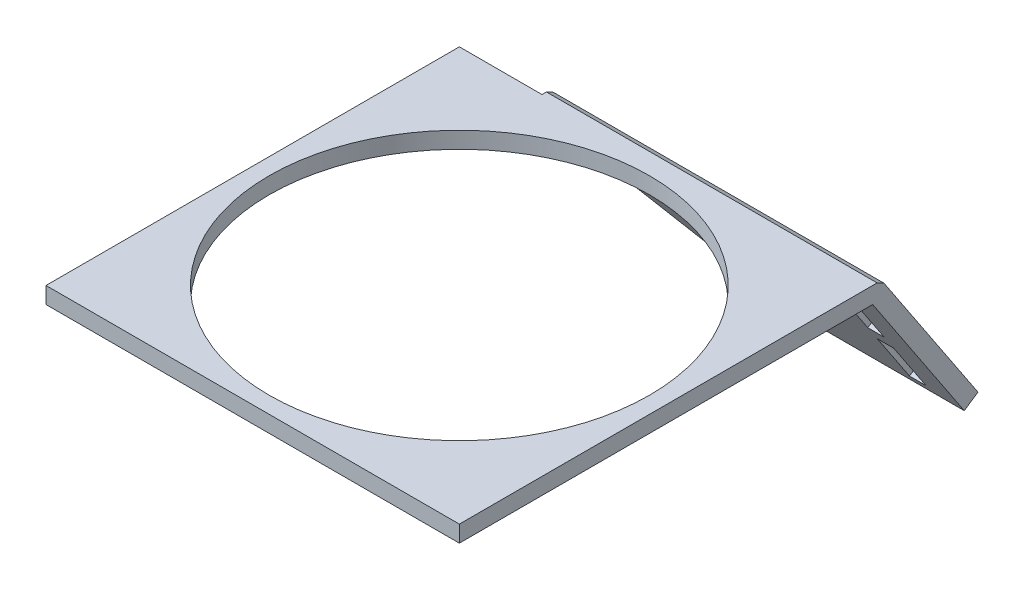
SolidWorks part; units mm, degrees
ref_plane "Front Plane" through (0, 0, 0) normal (0, 0, 1) x (1, 0, 0)
ref_plane "Top Plane" through (0, 0, 0) normal (0, 1, 0) x (1, 0, 0)
ref_plane "Right Plane" through (0, 0, 0) normal (1, 0, 0) x (0, 0, -1)
sketch "Sketch1" plane through (0, 0, 0) normal (0, 1, 0) x (1, 0, 0)
  line L0 (-40, 15.1776) -> (0, -24.8224) construction
  line L1 (-40, 15.1776) -> (0, 15.1776)
  line L2 (-40, 15.1776) -> (-40, -24.8224)
  line L3 (-40, -24.8224) -> (0, -24.8224)
  line L4 (0, 15.1776) -> (0, -24.8224)
  line L5 (0, -24.8224) -> (-0.0735, -24.5293) construction
  circle A0 centre (-20, -4.8224) radius 19
  dimension "D3" = 38
  dimension "D1" = 40
  dimension "D2" = 40
extrude "Boss-Extrude1" add sketch "Sketch1" along normal blind 1
sketch "Sketch2" plane through (0, 0, 0) normal (1, 0, 0) x (0, 0, -1)
  line L0 (15.1776, 0) -> (26.2516, -16.6543)
  line L1 (26.2516, -16.6543) -> (27.0843, -16.1006)
  line L2 (27.0843, -16.1006) -> (15.7136, 1)
  line L3 (15.7136, 1) -> (15.1776, 1)
  line L4 (15.1776, 1) -> (15.1776, 0)
  dimension "D1" = 1
  dimension "D2" = 1
  dimension "D3" = 20
extrude "Boss-Extrude3" add sketch "Sketch2" against normal blind 40
sketch "Sketch3" plane through (0, 6.998, -10.5244) normal (0, -0.5537, 0.8327) x (1, 0, 0)
  line L0 (-20, -28.4038) -> (-40, -8.4038)
  line L1 (-40, -28.4038) -> (0, -28.4038) construction
  line L2 (-40, -8.4038) -> (-40, -28.4038)
  line L3 (-40, -28.4038) -> (-20, -28.4038)
extrude "Cut-Extrude1" cut sketch "Sketch3" against normal blind 40
sketch "Sketch4" plane through (0, 6.998, -10.5244) normal (0, -0.5537, 0.8327) x (1, 0, 0)
  line L0 (-5, -8.4038) -> (-5, -28.4038) construction
  line L1 (0, -8.4038) -> (-40, -8.4038) construction
  line L2 (-20, -28.4038) -> (0, -28.4038) construction
  line L3 (0, -8.4038) -> (0, -28.4038) construction
  line L5 (-4, -27.2711) -> (-6, -27.2711)
  line L6 (-4, -27.2711) -> (-4, -9.3119)
  line L7 (-4, -9.3119) -> (-6, -9.3119)
  line L8 (-6, -27.2711) -> (-6, -9.3119)
  dimension "D1" = 5
  dimension "D2" = 1
  dimension "D3" = 1
extrude "Cut-Extrude2" cut sketch "Sketch4" against normal blind 40
sketch "Sketch5" plane through (0, 6.998, -10.5244) normal (0, -0.5537, 0.8327) x (1, 0, 0)
  line L1 (-3.0456, -20.2228) -> (-7.3369, -20.2228)
  line L2 (-3.0456, -20.2228) -> (-3.0456, -18.1628)
  line L3 (-3.0456, -18.1628) -> (-7.3369, -18.1628)
  line L4 (-7.3369, -20.2228) -> (-7.3369, -18.1628)
extrude "Boss-Extrude4" add sketch "Sketch5" against normal blind 1
sketch "Sketch6" plane through (0, 1, 0) normal (0, 1, 0) x (1, 0, 0)
  line L1 (-40, -24.8224) -> (0, -24.8224)
  line L2 (-40, -24.8224) -> (-40, 15.7136)
  line L3 (-40, 15.7136) -> (0, 15.7136)
  line L4 (0, -24.8224) -> (0, 15.7136)
  circle A0 centre (-20, -4.8224) radius 19
extrude "Boss-Extrude5" add sketch "Sketch6" along normal blind 1
sketch "Sketch7" plane through (0, 7.5517, -11.3571) normal (0, 0.5537, -0.8327) x (-1, 0, 0)
  line L0 (40, -7.8679) -> (40, -8.4038)
  line L1 (40, -8.4038) -> (20, -28.4038)
  line L2 (20, -28.4038) -> (0, -28.4038)
  line L3 (0, -28.4038) -> (0, -7.8679)
  line L4 (0, -7.8679) -> (40, -7.8679)
  line L6 (6, -9.3119) -> (4, -9.3119)
  line L7 (6, -9.3119) -> (6, -18.1628)
  line L8 (6, -18.1628) -> (4, -18.1628)
  line L9 (4, -9.3119) -> (4, -18.1628)
  line L10 (6, -20.2228) -> (4, -20.2228)
  line L11 (6, -20.2228) -> (6, -27.2711)
  line L12 (6, -27.2711) -> (4, -27.2711)
  line L13 (4, -20.2228) -> (4, -27.2711)
extrude "Boss-Extrude6" add sketch "Sketch7" along normal blind 1
sketch "Sketch8" plane through (0, 0, 0) normal (1, 0, 0) x (0, 0, -1)
  line L0 (15.7136, 2) -> (16.5463, 1.5537)
  line L1 (16.5463, 1.5537) -> (15.7136, 1)
  line L2 (15.7136, 1) -> (15.7136, 2)
extrude "Boss-Extrude7" add sketch "Sketch8" against normal up to surface (40 mm away) up to face at (-40, 1.0944, -4.3356)
sketch "Sketch9" plane through (0, 0, 0) normal (0, -1, 0) x (-1, 0, 0)
  line L1 (0, 15.1776) -> (50, 15.1776)
  line L2 (0, 15.1776) -> (0, -34.8224)
  line L3 (0, -34.8224) -> (50, -34.8224)
  line L4 (50, 15.1776) -> (50, -34.8224)
  dimension "D1" = 50
  dimension "D2" = 50
extrude "Boss-Extrude8" add sketch "Sketch9" against normal blind 2
sketch "Sketch10" plane through (0, 0, 0) normal (0, -1, 0) x (-1, 0, 0)
  line L0 (0, 15.1776) -> (50, -34.8224) construction
  circle A0 centre (25, -9.8224) radius 23
  dimension "D1" = 46
extrude "Cut-Extrude3" cut sketch "Sketch10" against normal blind 2
